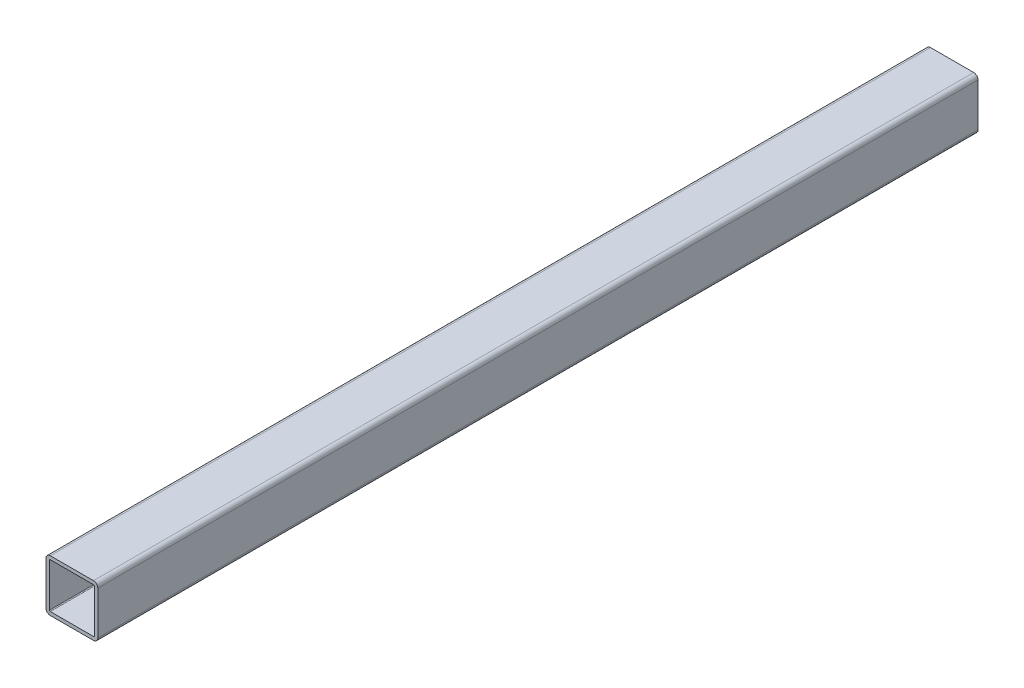
SolidWorks part; units mm, degrees
ref_plane "Front Plane" through (0, 0, 0) normal (0, 0, 1) x (1, 0, 0)
ref_plane "Top Plane" through (0, 0, 0) normal (0, 1, 0) x (1, 0, 0)
ref_plane "Right Plane" through (0, 0, 0) normal (1, 0, 0) x (0, 0, -1)
sketch "Sketch1" plane through (0, 0, 0) normal (0, 0, 1) x (1, 0, 0)
  line L1 (-15.875, 19.05) -> (15.875, 19.05)
  line L2 (-19.05, 15.875) -> (-19.05, -15.875)
  line L3 (-15.875, -19.05) -> (15.875, -19.05)
  line L4 (19.05, 15.875) -> (19.05, -15.875)
  line L5 (-19.05, 19.05) -> (19.05, -19.05) construction
  line L6 (-19.05, -19.05) -> (19.05, 19.05) construction
  arc A0 (-19.05, -15.875) -> (-15.875, -19.05) centre (-15.875, -15.875) ccw
  arc A1 (15.875, -19.05) -> (19.05, -15.875) centre (15.875, -15.875) ccw
  arc A2 (19.05, 15.875) -> (15.875, 19.05) centre (15.875, 15.875) ccw
  arc A3 (-15.875, 19.05) -> (-19.05, 15.875) centre (-15.875, 15.875) ccw
  point P0 (0, 0)
  dimension "D3" = 3.175
  dimension "D1" = 38.1
  dimension "D2" = 38.1
extrude "Extrude-Thin1" add sketch "Sketch1" along normal mid plane 647.7 thin
sketch "Sketch3" plane through (19.05, 0, 0) normal (1, 0, 0) x (0, 0, -1)
  line L0 (323.85, 0) -> (-323.85, 0) construction
  line L1 (323.85, -15.875) -> (323.85, 15.875) construction
  line L2 (-323.85, -15.875) -> (-323.85, 15.875) construction
  line L3 (304.8, 19.05) -> (304.8, -19.05) construction
  line L4 (-323.85, 19.05) -> (323.85, 19.05) construction
  line L5 (-323.85, -19.05) -> (323.85, -19.05) construction
  line L6 (-304.8, 19.05) -> (-304.8, -19.05) construction
  line L7 (-228.6, 19.05) -> (-228.6, -19.05) construction
  line L8 (-152.4, 19.05) -> (-152.4, -19.05) construction
  line L9 (-76.2, 19.05) -> (-76.2, -19.05) construction
  dimension "D1" = 19.05
  dimension "D2" = 19.05
  dimension "D3" = 76.2
  dimension "D4" = 76.2
  dimension "D5" = 76.2
sketch "Sketch4" plane through (-19.05, 0, 0) normal (-1, 0, 0) x (0, 0, 1)
  line L0 (323.85, 0) -> (-323.85, 0) construction
  line L1 (323.85, 15.875) -> (323.85, -15.875) construction
  line L2 (-323.85, 15.875) -> (-323.85, -15.875) construction
  line L3 (-304.8, 19.05) -> (-304.8, -19.05) construction
  line L4 (323.85, 19.05) -> (-323.85, 19.05) construction
  line L5 (323.85, -19.05) -> (-323.85, -19.05) construction
  line L6 (76.2, 19.05) -> (76.2, -19.05) construction
  line L7 (152.4, 19.05) -> (152.4, -19.05) construction
  line L8 (228.6, 19.05) -> (228.6, -19.05) construction
  line L9 (304.8, 19.05) -> (304.8, -19.05) construction
  line L10 (0, 19.05) -> (0, -19.05) construction
  line L11 (-76.2, 19.05) -> (-76.2, -19.05) construction
  line L12 (-152.4, 19.05) -> (-152.4, -19.05) construction
  line L13 (-228.6, 19.05) -> (-228.6, -19.05) construction
  dimension "D1" = 19.05
  dimension "D2" = 76.2
  dimension "D3" = 76.2
  dimension "D4" = 76.2
  dimension "D5" = 19.05
  dimension "D6" = 76.2
  dimension "D7" = 76.2
  dimension "D8" = 76.2
  dimension "D9" = 76.2
